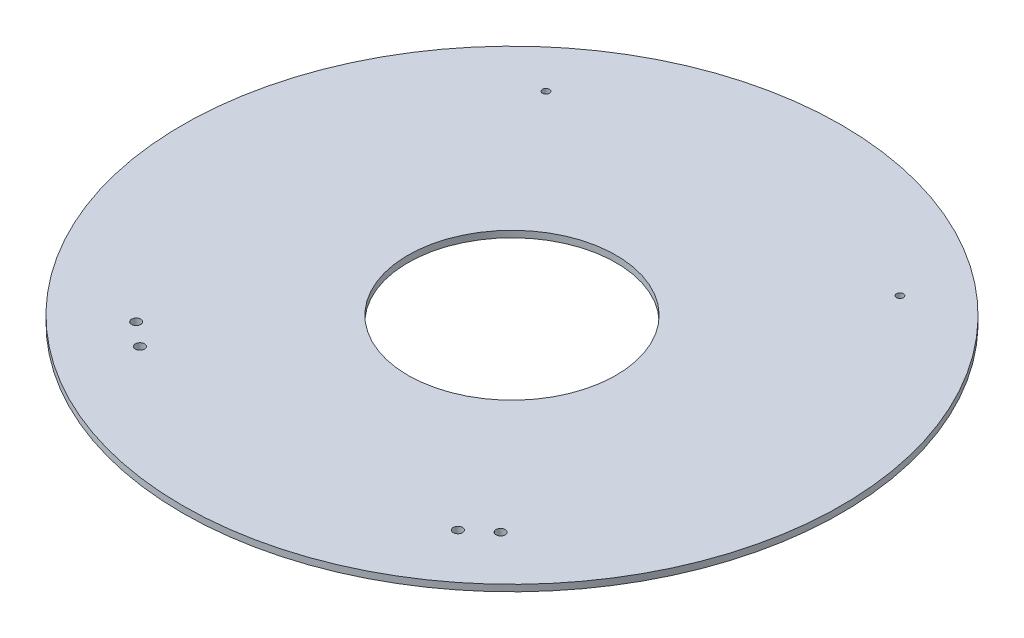
SolidWorks part; units mm, degrees
material "PC High Viscosity"
ref_plane "Front Plane" through (0, 0, 0) normal (0, 0, 1) x (1, 0, 0)
ref_plane "Top Plane" through (0, 0, 0) normal (0, 1, 0) x (1, 0, 0)
ref_plane "Right Plane" through (0, 0, 0) normal (1, 0, 0) x (0, 0, -1)
sketch "Sketch1" plane through (0, 0, 0) normal (0, 1, 0) x (1, 0, 0)
  circle A0 centre (0, 0) radius 241.3
  circle A1 centre (0, 0) radius 76.2
  dimension "D1" = 482.6
  dimension "D2" = 152.4
extrude "Boss-Extrude1" add sketch "Sketch1" along normal blind 4.7625
hole_wizard "1/4 Clearance Hole1" positions "Sketch2" profile "Sketch3" hole size "1/4" standard "ANSI Inch" end condition through all
sketch "Sketch2" plane through (0, 0, 0) normal (0, -1, 0) x (-1, 0, 0)
  line L0 (0, 0) -> (0, -241.3) construction
  line L3 (-148.7315, -147.6148) -> (-119.5452, -172.105)
  line L4 (-148.7315, -147.6148) -> (-134.4456, -130.5895)
  line L5 (-119.5452, -172.105) -> (-105.2593, -155.0797)
  line L6 (-134.4456, -130.5895) -> (-105.2593, -155.0797)
  line L7 (-119.8524, -142.8346) -> (-134.1384, -159.8599) construction
  line L8 (-139.5069, -136.6213) -> (-110.3206, -161.1115)
  circle A0 centre (0, 0) radius 241.3 construction
  circle A1 centre (0, 0) radius 209.55
  point P221 (-133.4264, -141.7234)
  point P223 (-116.4011, -156.0094)
  point P230 (0, 0)
  point P231 (-119.8524, -172.105)
  point P232 (116.4011, -156.0094)
  point P233 (133.4264, -141.7234)
  dimension "D6" = 419.1
  dimension "D1" = 22.225
  dimension "D2" = 38.1
  dimension "D3" = 40
  dimension "D4" = 7.874
  dimension "D5" = 22.225
sketch "Sketch3" plane through (-133.4264, 0, 141.7234) normal (1, 0, 0) x (0, 0, -1)
  line L0 (0, 0) -> (0, 4.7625)
  line L1 (0, 4.7625) -> (3.3782, 4.7625)
  line L2 (3.3782, 4.7625) -> (3.3782, 0)
  line L5 (3.3782, 0) -> (0, 0)
  line L11 (0, -6.35) -> (0, 107.95) construction
  dimension "Thru Hole Dia." = 6.7564
  dimension "Thru Hole Depth" = 4.7625
hole_wizard "#10 Clearance Hole1" positions "Sketch4" profile "Sketch5" hole size "#10" standard "ANSI Inch" end condition through all
sketch "Sketch4" plane through (0, 0, 0) normal (0, -1, 0) x (-1, 0, 0)
  line L0 (0, 0) -> (0, 241.3) construction
  line L2 (0, 0) -> (-155.1047, 184.8465) construction
  circle A0 centre (0, 0) radius 241.3 construction
  circle A1 centre (0, 0) radius 209.55
  circle A2 centre (-129.594, 154.4441) radius 7.9375
  point P0 (-129.594, 154.4441)
  point P20 (129.594, 154.4441)
  dimension "D2" = 419.1
  dimension "D3" = 15.875
  dimension "D1" = 40
sketch "Sketch5" plane through (129.594, 0, -154.4441) normal (1, 0, 0) x (0, 0, -1)
  line L0 (0, 0) -> (0, 4.7625)
  line L1 (0, 4.7625) -> (2.5527, 4.7625)
  line L2 (2.5527, 4.7625) -> (2.5527, 0)
  line L5 (2.5527, 0) -> (0, 0)
  line L11 (0, -6.35) -> (0, 107.95) construction
  dimension "Thru Hole Dia." = 5.1054
  dimension "Thru Hole Depth" = 4.7625
